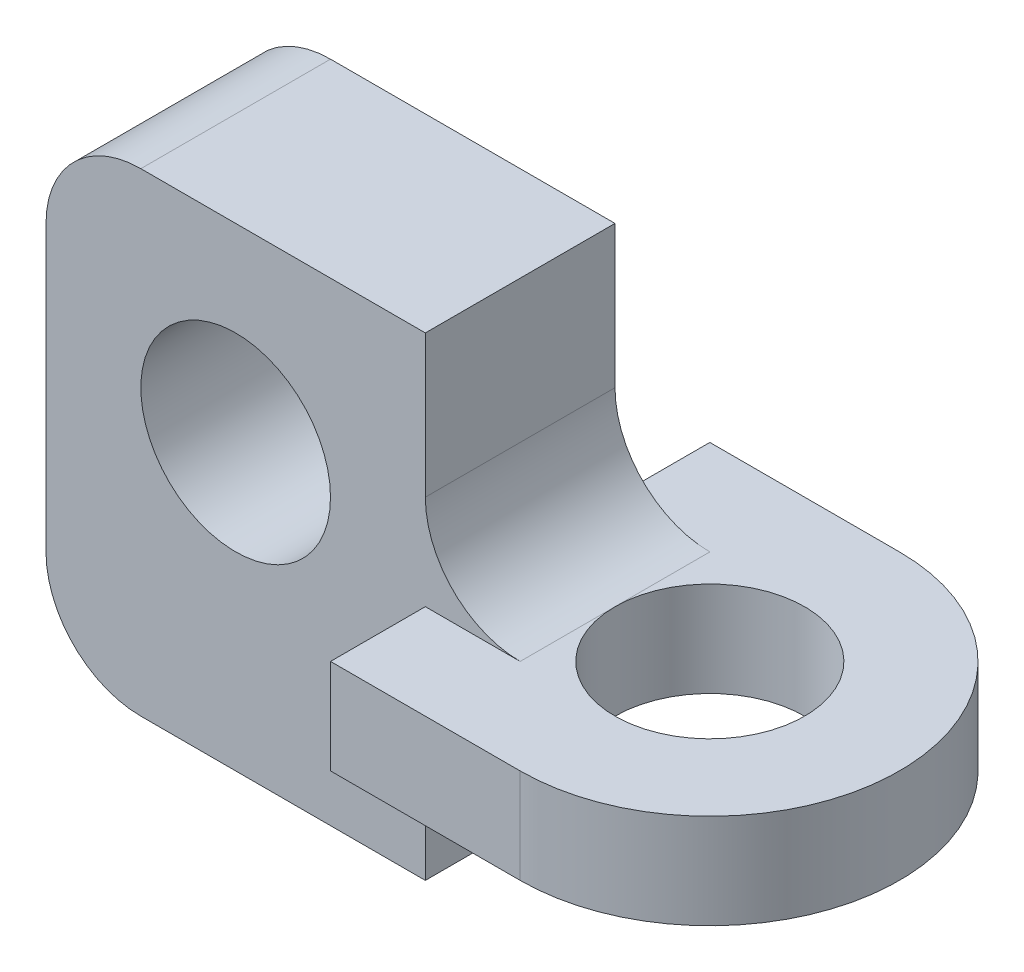
SolidWorks part; units mm, degrees
ref_plane "前基準面" through (0, 0, 0) normal (0, 0, 1) x (1, 0, 0)
ref_plane "上基準面" through (0, 0, 0) normal (0, 1, 0) x (1, 0, 0)
ref_plane "右基準面" through (0, 0, 0) normal (1, 0, 0) x (0, 0, -1)
sketch "草圖1" plane through (0, 0, 0) normal (0, 1, 0) x (1, 0, 0)
  line L0 (0, 10) -> (-10, 10)
  line L1 (-10, 10) -> (-10, -10)
  line L2 (-10, -10) -> (0, -10)
  circle A0 centre (0, 0) radius 5
  arc A1 (0, -10) -> (0, 10) centre (0, 0) ccw
  dimension "D1" = 20
  dimension "D2" = 10
extrude "填料-伸長1" add sketch "草圖1" along normal mid plane 5
sketch "草圖2" plane through (0, 0, 0) normal (0, 0, 1) x (1, 0, 0)
  line L0 (0, 0) -> (0, 5) construction
  line L1 (0, 5) -> (-20, 5) construction
  line L2 (-20, 5) -> (-20, -1.4071) construction
  line L3 (-30, 1.8983) -> (-30, -5)
  line L4 (-25, -10) -> (-10, -10)
  line L5 (-10, -10) -> (-10, -2.5)
  line L6 (-10, -2.5) -> (0, -2.5) construction
  line L7 (-30, 1.8983) -> (-30, 10)
  line L8 (-25, 15) -> (-10, 15)
  line L9 (-10, 15) -> (-10, 2.5)
  line L10 (-10, 2.5) -> (0, 2.5) construction
  line L11 (-10, 2.5) -> (-10, -2.5)
  circle A0 centre (-20, 5) radius 5
  arc A1 (-30, -5) -> (-25, -10) centre (-25, -5) ccw
  arc A2 (-30, 10) -> (-25, 15) centre (-25, 10) cw
  dimension "D3" = 10
  dimension "D4" = 10
  dimension "D7" = 5
  dimension "D1" = 5
  dimension "D2" = 20
  dimension "D5" = 10
  dimension "D6" = 15
extrude "填料-伸長2" add sketch "草圖2" along normal mid plane 10
fillet "圓角1" radius 5 2 edges at (-10, -2.5, 0) (-10, 2.5, 0)
scale "縮放比例1" scale about centroid uniform scaling yes scale factor 0.2
